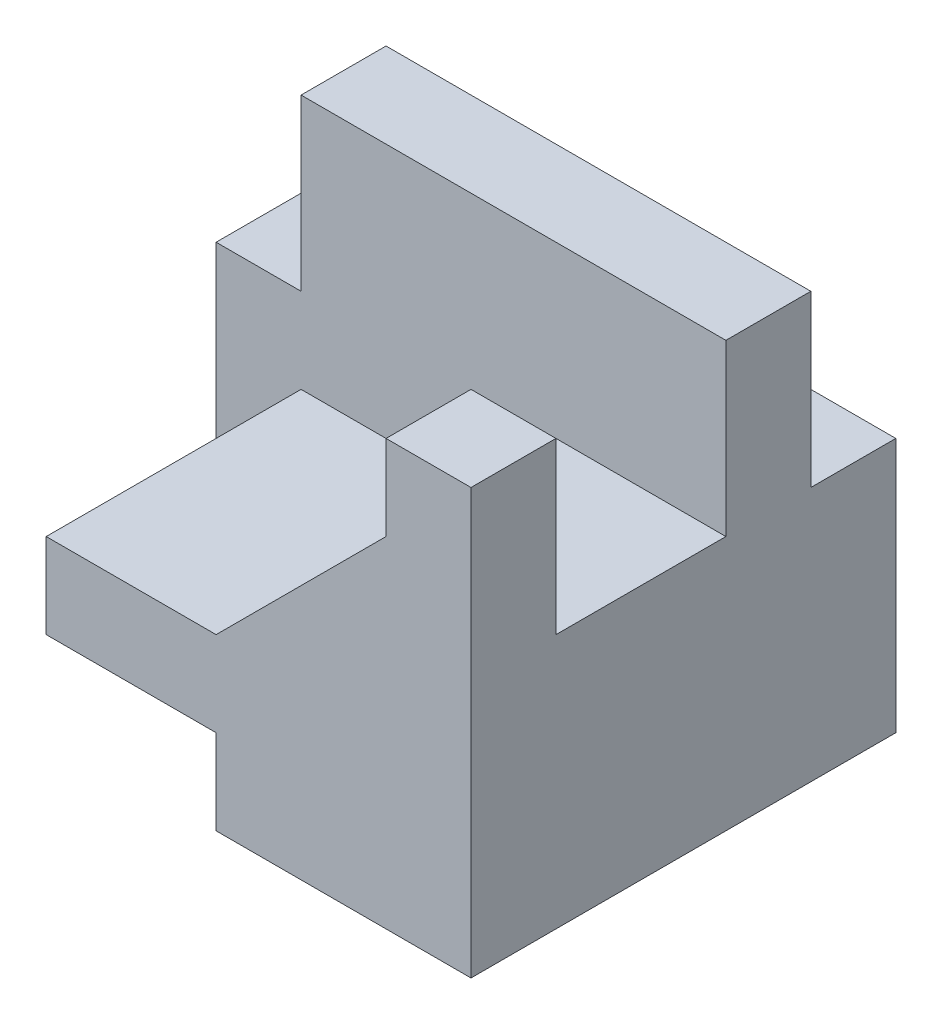
SolidWorks part; units mm, degrees
ref_plane "Front Plane" through (0, 0, 0) normal (0, 0, 1) x (1, 0, 0)
ref_plane "Top Plane" through (0, 0, 0) normal (0, 1, 0) x (1, 0, 0)
ref_plane "Right Plane" through (0, 0, 0) normal (1, 0, 0) x (0, 0, -1)
sketch "Sketch1" plane through (0, 0, 0) normal (0, 0, 1) x (1, 0, 0)
  line L0 (0, 0) -> (15, 0)
  line L1 (15, 0) -> (15, 25)
  line L2 (15, 25) -> (10, 25)
  line L3 (10, 25) -> (10, 20)
  line L4 (10, 20) -> (0, 10)
  line L5 (0, 10) -> (-10, 10)
  line L6 (-10, 10) -> (-10, 5)
  line L7 (-10, 5) -> (0, 5)
  line L8 (0, 5) -> (0, 0)
  dimension "D1" = 5
  dimension "D2" = 10
  dimension "D3" = 5
  dimension "D4" = 10
  dimension "D5" = 5
  dimension "D6" = 5
  dimension "D7" = 10
  dimension "D8" = 10
extrude "Boss-Extrude1" add sketch "Sketch1" along normal blind 15
sketch "Sketch2" plane through (0, 0, 0) normal (0, 0, -1) x (-1, 0, 0)
  line L1 (-15, 0) -> (15, 0)
  line L2 (-15, 0) -> (-15, 25)
  line L3 (-15, 25) -> (15, 25)
  line L4 (15, 0) -> (15, 25)
  dimension "D1" = 25
  dimension "D2" = 30
extrude "Boss-Extrude2" add sketch "Sketch2" along normal blind 10
sketch "Sketch3" plane through (0, 0, 0) normal (0, 0, 1) x (1, 0, 0)
  line L1 (-15, 25) -> (-10, 25)
  line L2 (-15, 25) -> (-15, 15)
  line L3 (-15, 15) -> (-10, 15)
  line L4 (-10, 25) -> (-10, 15)
  dimension "D1" = 10
  dimension "D2" = 5
extrude "Cut-Extrude1" cut sketch "Sketch3" against normal blind 15
sketch "Sketch6" plane through (-10, 0, 0) normal (-1, 0, 0) x (0, 0, 1)
  line L0 (-10, 25) -> (0, 25) construction
  line L1 (-10, 15) -> (-5, 15)
  line L2 (-10, 15) -> (-10, 25)
  line L3 (-10, 25) -> (-5, 25)
  line L4 (-5, 15) -> (-5, 25)
extrude "Cut-Extrude4" cut sketch "Sketch6" against normal blind 30
sketch "Sketch7" plane through (-10, 0, 0) normal (-1, 0, 0) x (0, 0, 1)
  line L1 (0, 25) -> (10, 25)
  line L2 (0, 25) -> (0, 15)
  line L3 (0, 15) -> (10, 15)
  line L4 (10, 25) -> (10, 15)
  dimension "D1" = 10
  dimension "D2" = 10
extrude "Cut-Extrude5" cut sketch "Sketch7" against normal blind 30
